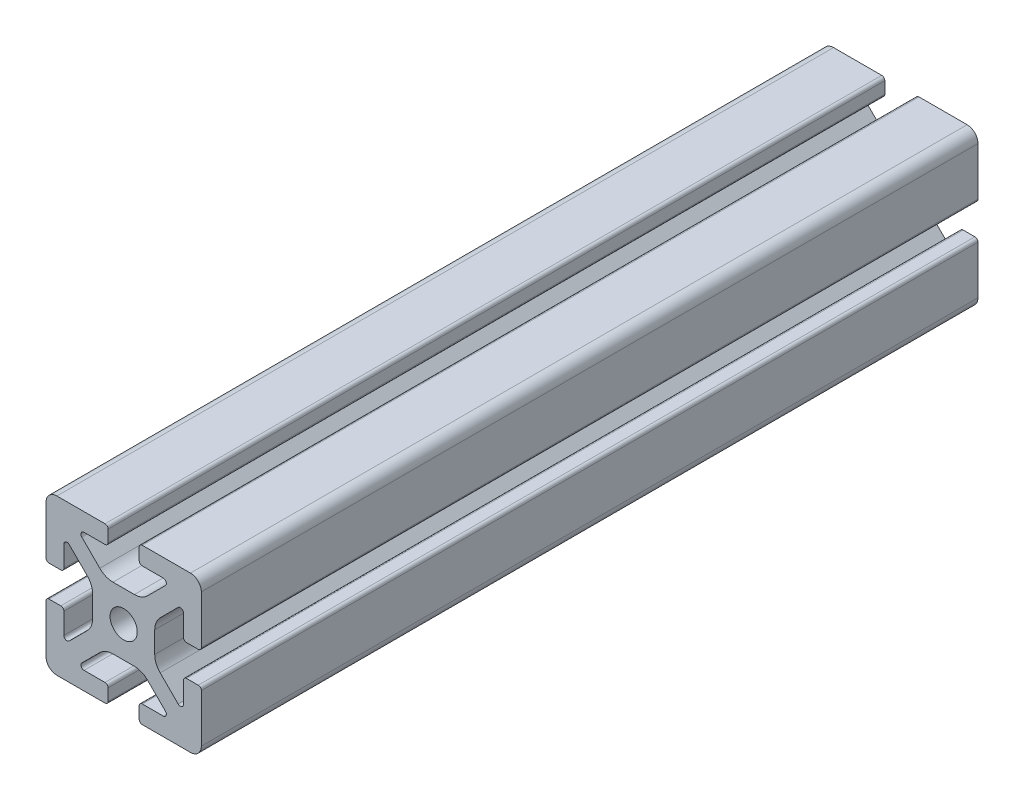
SolidWorks part; units mm, degrees
material "6061-T6 (SS)"
ref_plane "Front Plane" through (0, 0, 0) normal (0, 0, 1) x (1, 0, 0)
ref_plane "Top Plane" through (0, 0, 0) normal (0, 1, 0) x (1, 0, 0)
ref_plane "Right Plane" through (0, 0, 0) normal (1, 0, 0) x (0, 0, -1)
sketch "Sketch2" plane through (0, 0, 0) normal (0, 0, 1) x (1, 0, 0)
  line L0 (0, 20) -> (0, -20) construction
  line L1 (-20, 0) -> (20, 0) construction
  line L2 (4, -20) -> (20, -20)
  line L3 (20, -20) -> (20, -4)
  line L4 (4, -20) -> (4, -15.3907)
  line L5 (4, -15.3907) -> (12.1314, -15.3907)
  line L6 (12.1314, -15.3907) -> (4.7407, -8)
  line L7 (0, 0) -> (20, -20) construction
  line L8 (20, -4) -> (15.3907, -4)
  line L9 (15.3907, -4) -> (15.3907, -12.1314)
  line L10 (15.3907, -12.1314) -> (8, -4.7407)
  line L11 (11.6953, -8.436) -> (8.436, -11.6953) construction
  circle A0 centre (0, 0) radius 3.5
  arc A1 (10.2, -15.3907) -> (10.7657, -14.025) centre (10.2, -14.5907) ccw construction
  point P8 (0, -8)
  point P16 (10.0657, -10.0657)
  dimension "Center Hole Diameter" = 7
  dimension "D3" = 0.8
  dimension "Rail Height" = 40
  dimension "Rail Width" = 40
  dimension "T-Slot Width" = 8
  dimension "Slot Depth" = 12
  dimension "Slot Inner Width" = 22
sketch "Sketch3" plane through (0, 0, 0) normal (1, 0, 0) x (0, 0, -1)
  line L0 (-457.2, -20) -> (457.2, -20) construction
  line L1 (-431.8, 0) -> (431.8, 0) construction
  line L2 (0, 20) -> (0, -20) construction
  line L3 (0, 20) -> (0, -20) construction
  point P6 (-431.8, 0)
  point P8 (431.8, 0)
  dimension "Length" = 914.4
  dimension "D1" = 25.4
sketch "Sketch4" plane through (0, 0, 0) normal (0, 0, 1) x (1, 0, 0)
  line L0 (4.8, -20) -> (17.2, -20)
  line L1 (4, -20) -> (20, -20) construction
  line L2 (4, -20) -> (4, -15.3907) construction
  line L3 (4, -15.3907) -> (12.1314, -15.3907) construction
  line L4 (4, -16.1907) -> (4, -19.2)
  line L5 (4.8, -15.3907) -> (10.2, -15.3907)
  line L6 (0, -8) -> (2.7525, -8)
  line L7 (12.1314, -15.3907) -> (4.7407, -8) construction
  line L8 (6.1466, -9.4059) -> (10.7657, -14.025)
  line L9 (20, -20) -> (20, -4) construction
  line L10 (15.3907, -12.1314) -> (8, -4.7407) construction
  line L11 (15.3907, -4) -> (15.3907, -12.1314) construction
  line L12 (15.3907, -10.2) -> (15.3907, -4.8)
  line L13 (20, -4) -> (15.3907, -4) construction
  line L14 (16.1907, -4) -> (19.2, -4)
  line L15 (20, -4.8) -> (20, -17.2)
  line L16 (14.025, -10.7657) -> (9.4059, -6.1466)
  line L17 (8, 0) -> (8, -2.7525)
  line L18 (-20, 0) -> (20, 0) construction
  line L19 (0, -8) -> (0, -3.5)
  line L20 (0, 20) -> (0, -20) construction
  line L21 (8, 0) -> (3.5, 0)
  arc A0 (4, -19.2) -> (4.8, -20) centre (4.8, -19.2) ccw
  arc A1 (10.2, -15.3907) -> (10.7657, -14.025) centre (10.2, -14.5907) ccw construction
  arc A2 (4, -16.1907) -> (4.8, -15.3907) centre (4.8, -16.1907) cw
  arc A3 (10.2, -15.3907) -> (10.7657, -14.025) centre (10.2, -14.5907) ccw
  arc A4 (2.7525, -8) -> (6.1466, -9.4059) centre (2.7525, -12.8) cw
  arc A5 (17.2, -20) -> (20, -17.2) centre (17.2, -17.2) ccw
  arc A6 (14.025, -10.7657) -> (15.3907, -10.2) centre (14.5907, -10.2) ccw
  arc A7 (15.3907, -4.8) -> (16.1907, -4) centre (16.1907, -4.8) cw
  arc A8 (19.2, -4) -> (20, -4.8) centre (19.2, -4.8) cw
  arc A9 (9.4059, -6.1466) -> (8, -2.7525) centre (12.8, -2.7525) cw
  circle A10 centre (0, 0) radius 3.5 construction
  arc A11 (0, -3.5) -> (3.5, 0) centre (0, 0) ccw
  dimension "D1" = 2.8
  dimension "D2" = 4.8
extrude "Boss-Extrude1" add sketch "Sketch4" along normal mid plane 200
mirror "Mirror1" about plane through (0, 0, 0) normal (1, 0, 0) of bodies 134
mirror "Mirror2" about plane through (0, 0, 0) normal (0, 1, 0) of bodies 135
equation "\"D3@Sketch2\"=\"T-Slot Width@Sketch2\"*0.1"
equation "\"D1@Sketch4\"=\"D3@Sketch2\"*3.5"
equation "\"D2@Sketch4\"=\"D3@Sketch2\"*6"
equation "\"D1@Boss-Extrude1\"=\"Length@Sketch3\""
